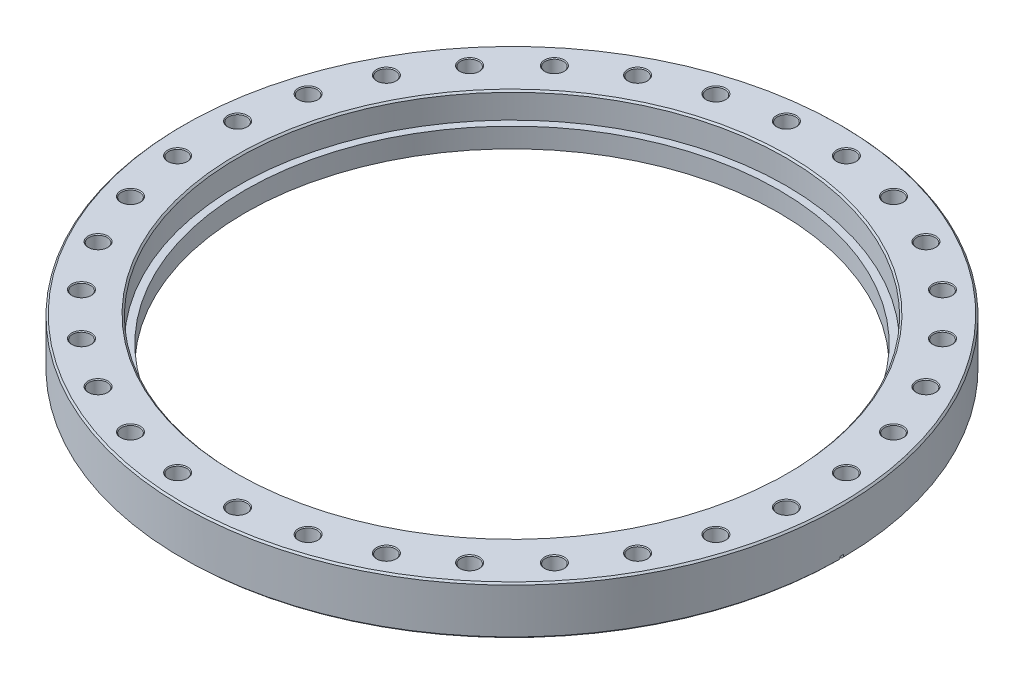
SolidWorks part; units mm, degrees
ref_plane "Front Plane" through (0, 0, 0) normal (0, 0, 1) x (1, 0, 0)
ref_plane "Top Plane" through (0, 0, 0) normal (0, 1, 0) x (1, 0, 0)
ref_plane "Right Plane" through (0, 0, 0) normal (1, 0, 0) x (0, 0, -1)
sketch "Sketch1" plane through (0, 0, 0) normal (0, 1, 0) x (1, 0, 0)
  circle A0 centre (0, 0) radius 152.9969
  circle A1 centre (0, 0) radius 123.825
  dimension "D1" = 305.9938
  dimension "D2" = 247.65
extrude "Boss-Extrude1" add sketch "Sketch1" along normal blind 22.352
sketch "Sketch2" plane through (0, 22.352, 0) normal (0, -1, 0) x (-1, 0, 0)
  circle A0 centre (0, 0) radius 127.254
  dimension "D1" = 254.508
extrude "Cut-Extrude1" cut sketch "Sketch2" along normal blind 11.938
chamfer "Chamfer1" distance 0.762 angle 45 3 edges at (0, 0, 152.9969) (0, 22.352, 152.9969) (0, 22.352, -127.254)
sketch "Sketch4" plane through (0, 0, 0) normal (0, 0, 1) x (1, 0, 0)
  line L0 (-137.16, 0) -> (-137.16, 1.6256)
  line L1 (-137.16, 1.6256) -> (-134.366, 0.6604)
  line L2 (-134.366, 0.6604) -> (-134.366, 1.27)
  line L3 (-134.366, 1.27) -> (0, 1.27)
  line L5 (0, 1.27) -> (0, 0)
  line L6 (0, 0) -> (-137.16, 0)
  dimension "D2" = 137.16
  dimension "D3" = 134.366
  dimension "D4" = 1.27
  dimension "D5" = 1.6256
  dimension "D6" = 0.6096
revolve "Cut-Revolve1" cut sketch "Sketch4" angle 360 about axis through (0, 22.352, 0) along (0, -1, 0)
sketch "Sketch3" plane through (0, 22.352, 0) normal (0, 1, 0) x (1, 0, 0)
  line L0 (0, 0) -> (-13.9183, 141.3149) construction
  line L1 (0, 0) -> (0, 152.2349) construction
  circle A0 centre (-13.9183, 141.3149) radius 4.2164
  circle A1 centre (0, 0) radius 152.2349 construction
  dimension "D2" = 8.4328
  dimension "D1" = 5.625
  dimension "D3" = 141.9987
extrude "Cut-Extrude2" cut sketch "Sketch3" against normal through all
chamfer "Chamfer2" distance 0.381 angle 45 2 edges at (-13.9183, 22.352, -137.0985) (-13.9183, 0, -137.0985)
pattern_circular "CirPattern1" count 32 every 11.25 about axis through (0, 0, 0) along (0, 1, 0) of "Cut-Extrude2", "Chamfer2"
sketch "Sketch5" plane through (0, 0, 0) normal (0, 0, 1) x (1, 0, 0)
  line L0 (-135.6761, 0.8887) -> (-152.9969, 1.7964)
  line L1 (-152.9969, 1.7964) -> (-152.9969, -6.2218)
  line L2 (-152.9969, -6.2218) -> (-135.6761, -6.2218)
  line L3 (0, -6.2218) -> (-135.6761, 0.8887) construction
  line L4 (-135.6761, 0.8887) -> (-135.6761, -6.2218)
  line L5 (-135.6761, -6.2218) -> (0, -6.2218) construction
  line L6 (135.6761, 0.8887) -> (135.6761, -6.2218)
  line L7 (152.9969, -6.2218) -> (135.6761, -6.2218)
  line L8 (0, -6.2218) -> (0, 0) construction
  line L9 (152.9969, 1.7964) -> (152.9969, -6.2218)
  line L10 (135.6761, 0.8887) -> (152.9969, 1.7964)
  dimension "D1" = 6.2218
  dimension "D3" = 3
extrude "Cut-Extrude3" cut sketch "Sketch5" against normal mid plane 1.5875
